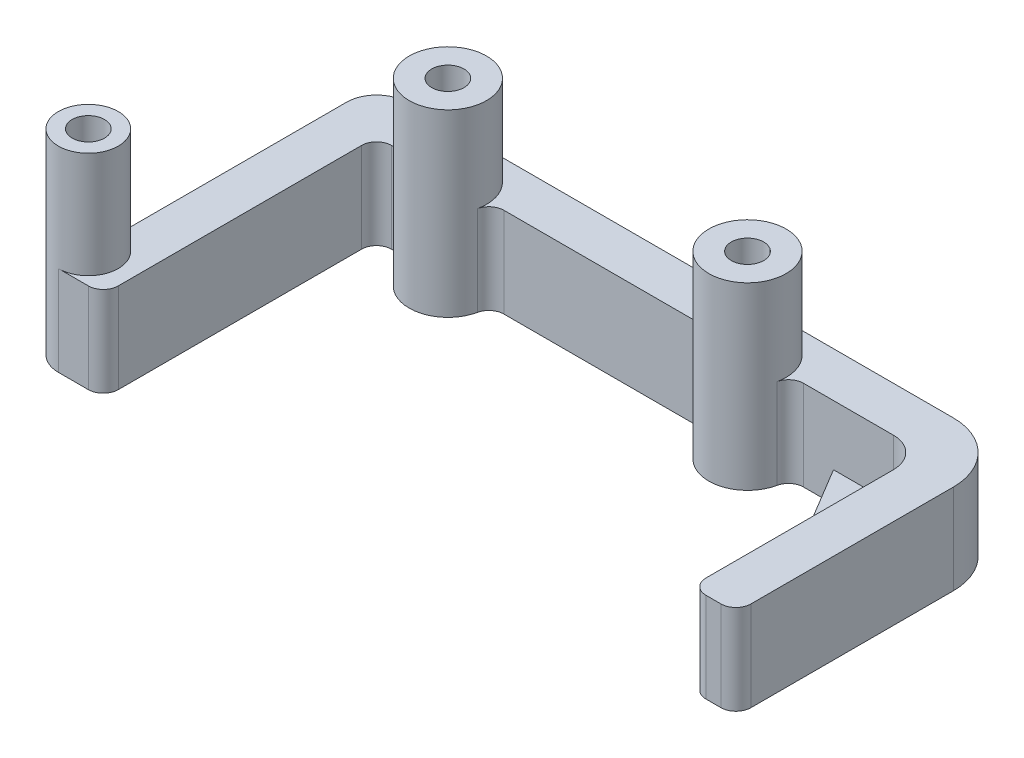
SolidWorks part; units mm, degrees
ref_plane "Front Plane" through (0, 0, 0) normal (0, 0, 1) x (1, 0, 0)
ref_plane "Top Plane" through (0, 0, 0) normal (0, 1, 0) x (1, 0, 0)
ref_plane "Right Plane" through (0, 0, 0) normal (1, 0, 0) x (0, 0, -1)
sketch "Sketch1" plane through (0, 0, 0) normal (0, 1, 0) x (-1, 0, 0)
  line L0 (-141.2875, 0) -> (0, 0)
  line L2 (0, 0) -> (0, 65.1236)
  line L5 (-141.2875, 65.1236) -> (-141.2875, 0)
  line L6 (0, 65.1236) -> (-141.2875, 65.1236)
  circle A0 centre (-134.9375, 16.6371) radius 2.667
  circle A9 centre (-134.9375, 42.0371) radius 2.667
  circle A10 centre (-134.9375, 67.4371) radius 2.667
  circle A11 centre (-122.2375, 16.6371) radius 2.667
  circle A12 centre (-109.5375, 16.6371) radius 2.667
  circle A13 centre (-96.8375, 16.6371) radius 2.667
  circle A14 centre (-84.1375, 16.6371) radius 2.667
  circle A15 centre (-71.4375, 16.6371) radius 2.667
  circle A16 centre (-58.7375, 16.6371) radius 2.667
  circle A17 centre (-46.0375, 16.6371) radius 2.667
  circle A18 centre (-33.3375, 16.6371) radius 2.667
  point P2 (0, 0)
  point P6 (0, 0)
  point P22 (0, 0)
  dimension "D1" = 5.334
  dimension "D4" = 25.4
  dimension "D5" = 25.4
  dimension "D6" = 9
  dimension "D7" = 12.7
  dimension "D2" = 65.1236
  dimension "D3" = 141.2875
  dimension "D8" = 6.35
  dimension "D9" = 16.6371
sketch "Sketch2" plane through (0, 0, 0) normal (0, 1, 0) x (1, 0, 0)
  line L1 (0, 0) -> (0, -65.1236) construction
  line L2 (57.1449, -15.875) -> (98.4301, -15.875)
  line L3 (120.6449, -15.875) -> (122.2375, -15.875)
  line L4 (134.9375, -73.7871) -> (128.5875, -73.7871)
  line L19 (0, -19.05) -> (0, -61.9486)
  line L20 (134.9375, -6.35) -> (0, -6.35)
  line L21 (134.9375, -65.1236) -> (134.9375, -6.35)
  line L22 (128.5875, -6.35) -> (12.7, -6.35)
  line L23 (134.9375, -58.4568) -> (134.9375, -12.7)
  line L27 (3.175, -65.1236) -> (6.35, -65.1236)
  line L28 (0, -65.1236) -> (141.2875, -65.1236) construction
  line L29 (9.525, -61.9486) -> (9.525, -22.225)
  line L30 (15.875, -15.875) -> (34.9301, -15.875)
  line L31 (125.4125, -19.05) -> (125.4125, -70.6121)
  arc A4 (134.9375, -12.7) -> (128.5875, -6.35) centre (128.5875, -12.7) ccw
  circle A6 centre (46.0375, -16.6371) radius 3.429
  circle A7 centre (109.5375, -16.6371) radius 3.429
  arc A8 (0, -19.05) -> (12.7, -6.35) centre (12.7, -19.05) cw
  arc A12 (6.35, -65.1236) -> (9.525, -61.9486) centre (6.35, -61.9486) ccw
  arc A15 (122.2375, -15.875) -> (125.4125, -19.05) centre (122.2375, -19.05) cw
  arc A16 (9.525, -22.225) -> (15.875, -15.875) centre (15.875, -22.225) cw
  arc A17 (3.175, -65.1236) -> (0, -61.9486) centre (3.175, -61.9486) cw
  arc A18 (38.0327, -18.376) -> (54.0423, -18.376) centre (46.0375, -16.6371) ccw
  arc A19 (101.5327, -18.376) -> (117.5423, -18.376) centre (109.5375, -16.6371) ccw
  circle A20 centre (46.0375, -16.6371) radius 8.1915 construction
  circle A21 centre (109.5375, -16.6371) radius 8.1915 construction
  arc A22 (38.0327, -18.376) -> (34.9301, -15.875) centre (34.9301, -19.05) ccw
  arc A23 (54.0423, -18.376) -> (57.1449, -15.875) centre (57.1449, -19.05) cw
  arc A24 (101.5327, -18.376) -> (98.4301, -15.875) centre (98.4301, -19.05) ccw
  arc A25 (117.5423, -18.376) -> (120.6449, -15.875) centre (120.6449, -19.05) cw
  circle A27 centre (134.9375, -67.4371) radius 3.429
  arc A29 (134.9375, -73.7871) -> (137.0542, -61.4502) centre (134.9375, -67.4371) ccw
  arc A30 (134.9375, -58.4568) -> (137.0542, -61.4502) centre (138.1125, -58.4568) ccw
  arc A31 (125.4125, -70.6121) -> (128.5875, -73.7871) centre (128.5875, -70.6121) ccw
  point P30 (0, -6.35)
  point P31 (0, -65.1236)
  point P42 (9.525, -65.1236)
  point P53 (54.1935, -15.875)
  point P58 (117.6935, -15.875)
  dimension "D1" = 6.35
  dimension "D2" = 6.35
  dimension "D3" = 9.525
  dimension "D7" = 9.525
  dimension "D4" = 6.858
  dimension "D9" = 12.7
  dimension "D10" = 3.175
  dimension "D6" = 3.175
  dimension "D12" = 3.175
  dimension "D13" = 3.175
  dimension "D14" = 6.35
  dimension "D11" = 6.35
  dimension "D5" = 4.7625
  dimension "D8" = 9.525
extrude "Boss-Extrude1" add sketch "Sketch2" against normal blind 19.05
sketch "Sketch3" plane through (0, 0, 0) normal (0, 1, 0) x (1, 0, 0)
  circle A0 centre (46.0375, -16.6371) radius 8.1915
  circle A1 centre (109.5375, -16.6371) radius 8.1915
  circle A2 centre (134.9375, -67.4371) radius 6.35
  circle A3 centre (46.0375, -16.6371) radius 3.429
  circle A4 centre (109.5375, -16.6371) radius 3.429
  circle A5 centre (134.9375, -67.4371) radius 3.429
  arc A6 (38.0327, -18.376) -> (54.0423, -18.376) centre (46.0375, -16.6371) ccw construction
  arc A7 (134.9375, -73.7871) -> (137.0542, -61.4502) centre (134.9375, -67.4371) ccw construction
  dimension "D2" = 6.858
extrude "Boss-Extrude2" add sketch "Sketch3" along normal blind 19.05
sketch "Sketch4" plane through (0, 19.05, 0) normal (0, 1, 0) x (1, 0, 0)
  circle A0 centre (134.9375, -67.4371) radius 3.429 construction
  circle A1 centre (134.9375, -67.4371) radius 6.35 construction
  circle A2 centre (134.9375, -67.4371) radius 3.429
  circle A3 centre (134.9375, -67.4371) radius 6.35
sketch "Sketch6" plane through (0, 0, 0) normal (0, 1, 0) x (1, 0, 0)
  line L0 (28.575, -15.875) -> (9.525, -47.625)
  line L2 (9.525, -47.625) -> (9.525, -15.875)
  line L3 (9.525, -15.875) -> (28.575, -15.875)
  line L5 (57.1449, -15.875) -> (98.4301, -15.875) construction
  line L6 (9.525, -61.9486) -> (9.525, -22.225) construction
  dimension "D1" = 19.05
  dimension "D2" = 31.75
extrude "Boss-Extrude5" add sketch "Sketch4" along normal blind 3.429
extrude "Boss-Extrude6" add sketch "Sketch6" along normal blind 6.35 from surface at -19.05 starting at face at (109.5375, -19.05, 20.0661)
mirror "Mirror4" about plane through (0, -19.05, 19.05) normal (-1, 0, 0) of "Boss-Extrude1", "Boss-Extrude2", "Boss-Extrude5", "Boss-Extrude6"
sketch "Sketch7" plane through (0, 0, 0) normal (0, 1, 0) x (1, 0, 0)
  line L6 (0, -6.35) -> (0, -73.7871)
  line L7 (0, -22.841) -> (0, 22.841) construction
  line L8 (0, -73.7871) -> (141.2875, -73.7871)
  line L9 (141.2875, -73.7871) -> (141.2875, -6.35)
  line L10 (141.2875, -6.35) -> (0, -6.35)
  line L11 (128.5875, -6.35) -> (12.7, -6.35) construction
  line L12 (128.5875, -73.7871) -> (134.9375, -73.7871) construction
  circle A0 centre (134.9375, -67.4371) radius 6.35 construction
extrude "Cut-Extrude2" cut sketch "Sketch7" along normal up to surface and the other way up to surface up to face at (134.9375, 22.479, 73.7871) other way up to face at (0, -19.05, 35.0388)
equation "\"D3\"=1.58333"
